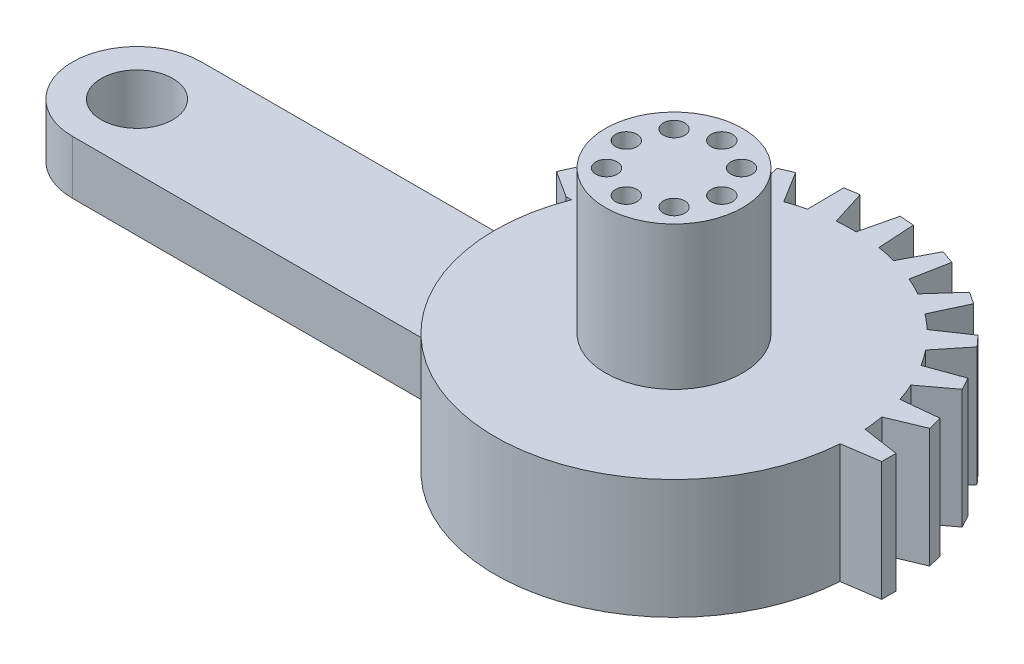
SolidWorks part; units mm, degrees
ref_plane "Front" through (0, 0, 0) normal (0, 0, 1) x (1, 0, 0)
ref_plane "Top" through (0, 0, 0) normal (0, 1, 0) x (1, 0, 0)
ref_plane "Right" through (0, 0, 0) normal (1, 0, 0) x (0, 0, -1)
sketch "Sketch1" plane through (0, 0, 0) normal (0, 1, 0) x (1, 0, 0)
  line L0 (-177.6425, 0) -> (70.7426, 0) construction
  line L1 (-150, 18) -> (-46.6476, 18)
  line L2 (-150, -18) -> (-46.6476, -18)
  arc A0 (-46.6476, -18) -> (-46.6476, 18) centre (0, 0) ccw
  arc A1 (-150, 18) -> (-150, -18) centre (-150, 0) ccw
  dimension "D1" = 100
  dimension "D3" = 150
  dimension "D2" = 18
extrude "Boss-Extrude1" add sketch "Sketch1" along normal blind 33.3333
sketch "Sketch2" plane through (0, 33.3333, 0) normal (0, 1, 0) x (1, 0, 0)
  line L0 (88.337, 0) -> (60, 0) construction
  line L1 (49.8773, 3.5) -> (60, 2)
  line L2 (60, 2) -> (60, -2)
  line L4 (50, 0) -> (49.8773, 3.5)
  line L5 (50, 0) -> (49.8773, -3.5)
  line L6 (49.8773, -3.5) -> (60, -2)
  line L7 (50, 0) -> (-74.3015, 0) construction
  line L8 (-46.6476, 18) -> (0, 0) construction
  arc A0 (-46.6476, -18) -> (-46.6476, 18) centre (0, 0) ccw construction
  arc A1 (49.8773, -3.5) -> (-46.6476, 18) centre (0, 0) ccw
  dimension "D1" = 4
  dimension "D2" = 10
  dimension "D3" = 3.5
extrude "Boss-Extrude2" add sketch "Sketch2" against normal up to surface (33.3333 mm away) contours L6 L2 L1 L4 L5 up to face at (-78.6619, 0, 0)
pattern_circular "CirPattern2" count 13 every 14.167 about axis through (0, 0, 0) along (0, 1, 0) of "Boss-Extrude2"
hole_wizard "Ø20.0mm 맞춤핀 구멍1" positions "Sketch4" profile "Sketch3" hole size "Ø20.0" standard "Ansi Metric" end condition through all
sketch "Sketch4" plane through (0, 33.3333, 0) normal (0, 1, 0) x (1, 0, 0)
  arc A0 (-150, 18) -> (-150, -18) centre (-150, 0) ccw construction
  point P0 (-150, 0)
  dimension "D1" = 0
sketch "Sketch3" plane through (-150, 33.3333, 0) normal (1, 0, 0) x (0, 0, 1)
  line L0 (0, 0) -> (0, 33.3333)
  line L1 (0, 33.3333) -> (10, 33.3333)
  line L2 (10, 33.3333) -> (10, 0)
  line L5 (10, 0) -> (0, 0)
  line L11 (0, -6.35) -> (0, 107.95) construction
  dimension "Thru Hole Dia." = 20
  dimension "Thru Hole Depth" = 33.3333
scale "축척1" scale about centroid uniform scaling yes scale factor 0.3
sketch "스케치1" plane through (0, 21.6667, 0) normal (0, 1, 0) x (1, 0, 0)
  line L0 (-36.0978, -4.0552) -> (-67.1035, -4.0552)
  line L2 (-36.5483, 6.7448) -> (-67.1035, 6.7448) construction
  line L3 (-67.1035, 6.7448) -> (-36.0978, 6.7448)
  arc A0 (-36.0978, 6.7448) -> (-36.0978, -4.0552) centre (-22.1035, 1.3448) ccw
  arc A1 (-67.1035, 6.7448) -> (-67.1035, -4.0552) centre (-67.1035, 1.3448) ccw construction
  arc A2 (-67.1035, 6.7448) -> (-67.1035, -4.0552) centre (-67.1035, 1.3448) ccw
  point P2 (0, 0)
  point P15 (0, 0)
extrude "컷-돌출1" cut sketch "스케치1" against normal blind 5.5
sketch "스케치2" plane through (0, 21.6667, 0) normal (0, 1, 0) x (1, 0, 0)
  circle A0 centre (-22.1035, 1.3448) radius 5.75
  dimension "D1" = 11.5
extrude "보스-돌출1" add sketch "스케치2" along normal blind 12
sketch "스케치3" plane through (0, 33.6667, 0) normal (0, 1, 0) x (1, 0, 0)
  line L0 (-22.1035, 1.3448) -> (-22.1035, -2.6552) construction
  line L1 (-22.1035, -2.6552) -> (-22.1035, 5.3448) construction
  line L2 (-22.1035, 5.3448) -> (-18.1035, 1.3448) construction
  line L3 (-18.1035, 1.3448) -> (-26.1035, 1.3448) construction
  line L4 (-22.1035, 1.3448) -> (-19.2751, 4.1732) construction
  line L5 (-19.2751, 4.1732) -> (-24.932, -1.4836) construction
  line L6 (-24.932, -1.4836) -> (-19.2751, -1.4836) construction
  line L7 (-19.2751, -1.4836) -> (-24.932, 4.1732) construction
  circle A0 centre (-22.1035, 1.3448) radius 4 construction
  circle A1 centre (-22.1035, -2.6552) radius 0.9
  circle A2 centre (-19.2751, -1.4836) radius 0.9
  circle A3 centre (-18.1035, 1.3448) radius 0.9
  circle A4 centre (-24.932, -1.4836) radius 0.9
  circle A5 centre (-26.1035, 1.3448) radius 0.9
  circle A6 centre (-24.932, 4.1732) radius 0.9
  circle A7 centre (-22.1035, 5.3448) radius 0.9
  circle A8 centre (-19.2751, 4.1732) radius 0.9
  dimension "D1" = 8
extrude "컷-돌출2" cut sketch "스케치3" against normal blind 7
